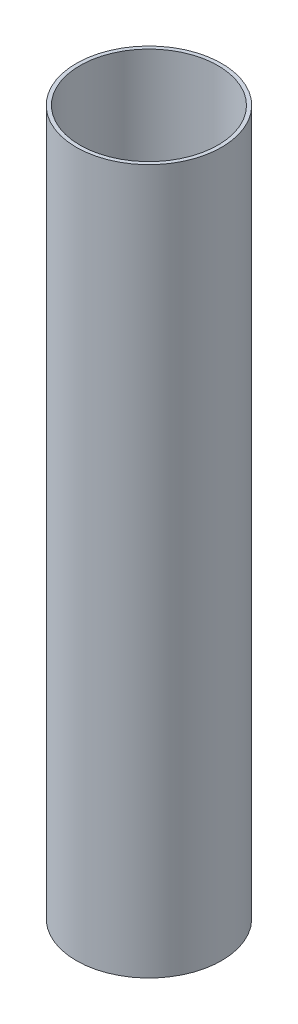
SolidWorks part; units mm, degrees
material "PVC Rigid"
ref_plane "Front Plane" through (0, 0, 0) normal (0, 0, 1) x (1, 0, 0)
ref_plane "Top Plane" through (0, 0, 0) normal (0, 1, 0) x (1, 0, 0)
ref_plane "Right Plane" through (0, 0, 0) normal (1, 0, 0) x (0, 0, -1)
sketch "Sketch1" plane through (0, 0, 0) normal (0, 1, 0) x (1, 0, 0)
  circle A0 centre (0, 0) radius 93.6625
  circle A1 centre (0, 0) radius 88.9
  dimension "D1" = 187.325
  dimension "D2" = 177.8
extrude "Boss-Extrude1" add sketch "Sketch1" along normal mid plane 907.6893
